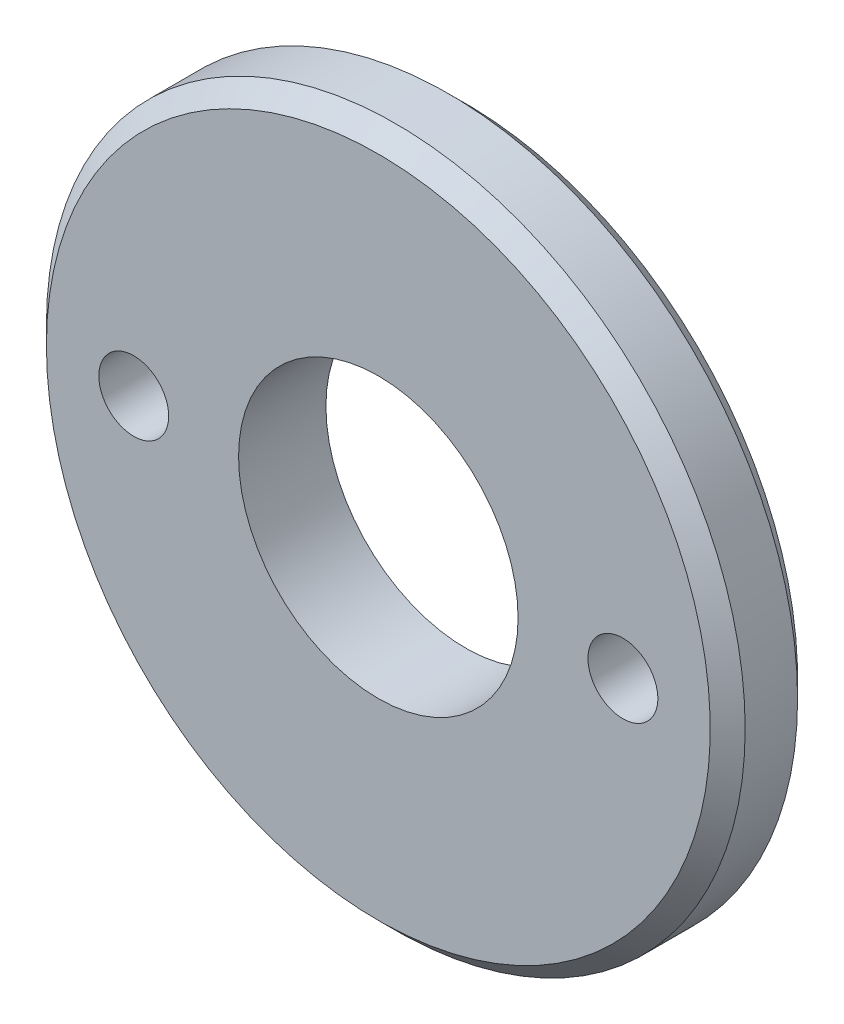
SolidWorks part; units mm, degrees
ref_plane "Front Plane" through (0, 0, 0) normal (0, 0, 1) x (1, 0, 0)
ref_plane "Top Plane" through (0, 0, 0) normal (0, 1, 0) x (1, 0, 0)
ref_plane "Right Plane" through (0, 0, 0) normal (1, 0, 0) x (0, 0, -1)
sketch "Sketch1" plane through (0, 0, 0) normal (0, 0, 1) x (1, 0, 0)
  circle A0 centre (0, 0) radius 12.5
  circle A1 centre (0, 0) radius 8
  dimension "D1" = 16
  dimension "D2" = 25
extrude "Boss-Extrude1" add sketch "Sketch1" along normal blind 2.5
cosmetic thread "Cosmetic Thread1" parameters "D2"=18
ref_plane "Plane1" through (0, -6, 0) normal (0, 1, 0) x (-1, 0, 0)
sketch "Sketch3" plane through (0, 0, 0) normal (0, 0, -1) x (-1, 0, 0)
  circle A0 centre (0, 0) radius 8
  circle A1 centre (0, 0) radius 20
  dimension "D1" = 40
extrude "Boss-Extrude3" add sketch "Sketch3" along normal blind 5
chamfer "Chamfer2" distance 1 angle 45 2 edges at (-20, 0, 0) (-20, 0, -5)
sketch "Sketch5" plane through (0, 0, 0) normal (0, 0, 1) x (1, 0, 0)
  circle A0 centre (0, 0) radius 12.5
extrude "Cut-Extrude1" cut sketch "Sketch5" along normal blind 10
sketch "Sketch6" plane through (0, 0, -5) normal (0, 0, -1) x (-1, 0, 0)
  circle A0 centre (14, 0) radius 2
  circle A1 centre (-14, 0) radius 2
  dimension "D1" = 4
  dimension "D2" = 4
  dimension "D3" = 14
  dimension "D4" = 14
  dimension "D5" = 0
extrude "Cut-Extrude2" cut sketch "Sketch6" against normal blind 5 from offset 2
